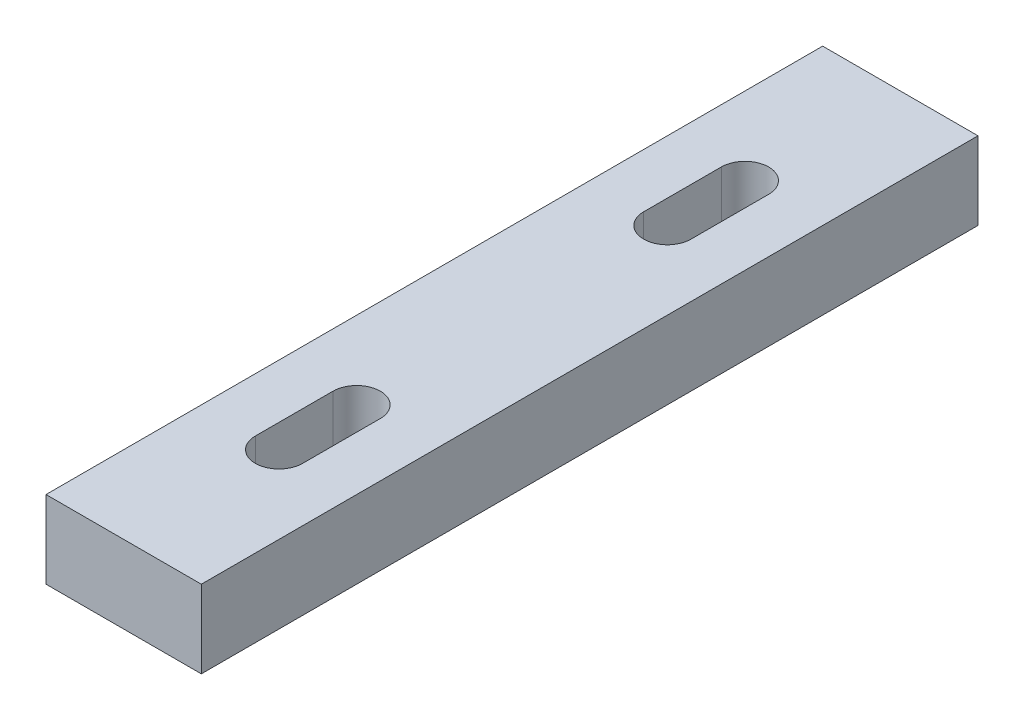
SolidWorks part; units mm, degrees
ref_plane "Front Plane" through (0, 0, 0) normal (0, 0, 1) x (1, 0, 0)
ref_plane "Top Plane" through (0, 0, 0) normal (0, 1, 0) x (1, 0, 0)
ref_plane "Right Plane" through (0, 0, 0) normal (1, 0, 0) x (0, 0, -1)
sketch "Sketch1" plane through (0, 0, 0) normal (0, 1, 0) x (1, 0, 0)
  line L1 (-10, 50) -> (10, 50)
  line L2 (-10, 50) -> (-10, -50)
  line L3 (-10, -50) -> (10, -50)
  line L4 (10, 50) -> (10, -50)
  line L5 (-10, 50) -> (10, -50) construction
  line L6 (-10, -50) -> (10, 50) construction
  point P0 (0, 0)
  dimension "D1" = 20
  dimension "D2" = 100
extrude "Boss-Extrude1" add sketch "Sketch1" along normal blind 10
sketch "Sketch2" plane through (0, 10, 0) normal (0, 1, 0) x (1, 0, 0)
  line L0 (0, 30) -> (0, 20) construction
  line L1 (0, -5.5) -> (0, 5.5) construction
  line L2 (3.05, 30) -> (3.05, 20)
  line L3 (-3.05, 30) -> (-3.05, 20)
  line L4 (-5.5, 0) -> (5.5, 0) construction
  arc A0 (3.05, 30) -> (-3.05, 30) centre (0, 30) ccw
  arc A1 (-3.05, 20) -> (3.05, 20) centre (0, 20) ccw
  point P5 (0, 25)
  dimension "D1" = 10
  dimension "D2" = 6.1
  dimension "D3" = 25
extrude "Cut-Extrude1" cut sketch "Sketch2" against normal up to surface (10 mm away) up to face at (0, 0, 0)
mirror "Mirror1" about plane through (0, 0, 0) normal (0, 0, 1) of "Cut-Extrude1"
